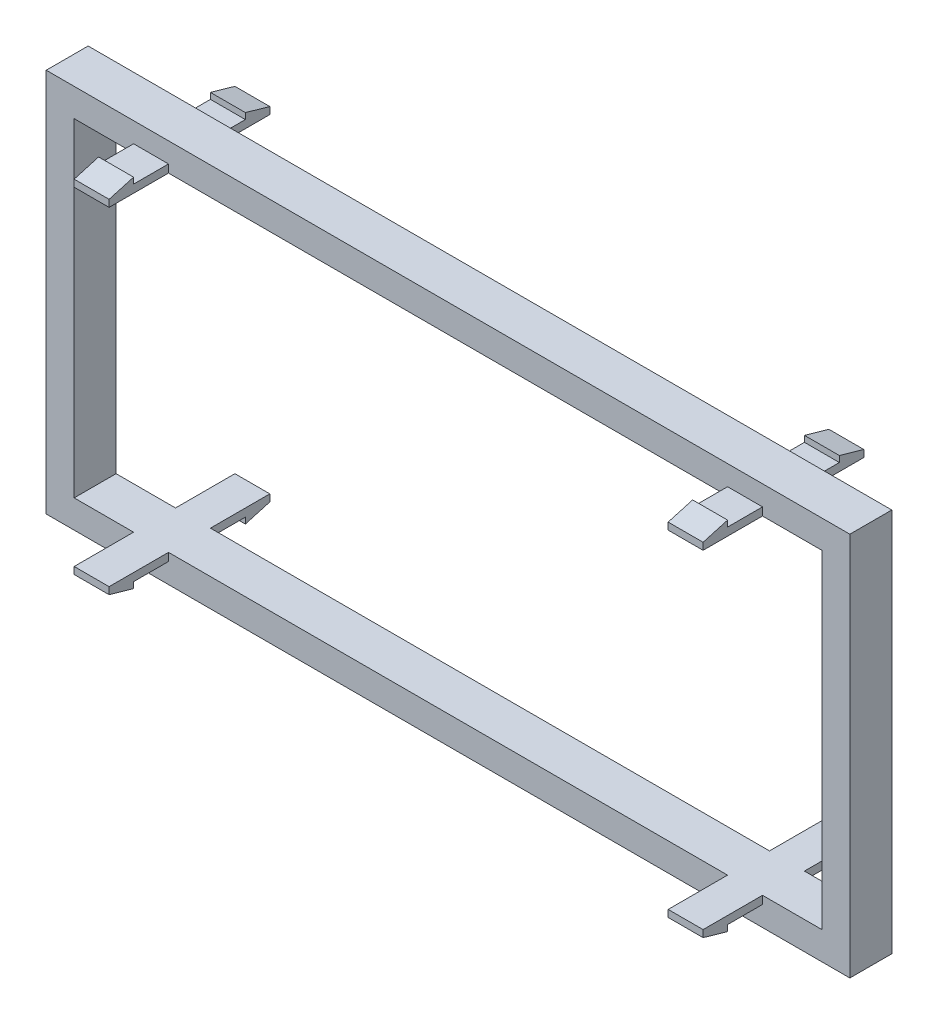
SolidWorks part; units mm, degrees
ref_plane "Front" through (0, 0, 0) normal (0, 0, 1) x (1, 0, 0)
ref_plane "Top" through (0, 0, 0) normal (0, 1, 0) x (1, 0, 0)
ref_plane "Right" through (0, 0, 0) normal (1, 0, 0) x (0, 0, -1)
sketch "Sketch1" plane through (0, 0, 0) normal (0, 0, 1) x (1, 0, 0)
  line L0 (0, 0) -> (0, 82.8716) construction
  line L1 (0, 0) -> (92.0509, 0) construction
  line L2 (-53.5, 23.5) -> (53.5, 23.5)
  line L3 (-57.5, 27.5) -> (57.5, 27.5)
  line L4 (-57.5, 27.5) -> (-57.5, -27.5)
  line L5 (-57.5, -27.5) -> (57.5, -27.5)
  line L6 (57.5, 27.5) -> (57.5, -27.5)
  line L7 (53.5, 23.5) -> (53.5, -23.5)
  line L8 (-53.5, -23.5) -> (53.5, -23.5)
  line L9 (-53.5, 23.5) -> (-53.5, -23.5)
  dimension "D1" = 115
  dimension "D2" = 55
  dimension "D3" = 4
extrude "Boss-Extrude1" add sketch "Sketch1" along normal blind 6
sketch "Sketch2" plane through (0, 0, 6) normal (0, 0, 1) x (1, 0, 0)
  line L0 (53.5, 23.5) -> (-53.5, 23.5) construction
  line L1 (-45, 25.5) -> (-40, 25.5)
  line L2 (-45, 25.5) -> (-45, 23.5)
  line L3 (-45, 23.5) -> (-40, 23.5)
  line L4 (-40, 25.5) -> (-40, 23.5)
  dimension "D1" = 2
  dimension "D2" = 45
  dimension "D3" = 40
extrude "Boss-Extrude2" add sketch "Sketch2" along normal blind 8.5
sketch "Sketch3" plane through (-40, 0, 0) normal (1, 0, 0) x (0, 0, -1)
  line L0 (-14.5, 24.5) -> (-11, 25.5)
  line L1 (-14.5, 23.5) -> (-14.5, 25.5) construction
  line L2 (-14.5, 25.5) -> (-6, 25.5) construction
  line L3 (-11, 25.5) -> (-11, 24.6338)
  line L4 (-11, 24.6338) -> (-6, 24.6338)
  line L5 (-6, 23.5) -> (-6, 25.5) construction
  line L6 (-6, 24.6338) -> (-6, 26.8746)
  line L7 (-6, -27.5) -> (-6, 27.5) construction
  line L8 (-6, 26.8746) -> (-14.5, 26.8746)
  line L9 (-14.5, 26.8746) -> (-14.5, 24.5)
  dimension "D1" = 5
extrude "Cut-Extrude1" cut sketch "Sketch3" against normal blind 10
mirror "Mirror1" about plane through (0, 0, 0) normal (0, 1, 0) of "Cut-Extrude1", "Boss-Extrude2"
mirror "Mirror2" about plane through (0, 0, 0) normal (1, 0, 0) of "Mirror1", "Boss-Extrude2", "Cut-Extrude1"
ref_plane "Plane1" through (0, 0, 3) normal (0, 0, 1) x (1, 0, 0)
mirror "Mirror3" about plane through (0, 0, 3) normal (0, 0, 1) of "Mirror2", "Boss-Extrude2", "Cut-Extrude1", "Mirror1"
sketch "Sketch4" plane through (0, 0, 0) normal (0, 1, 0) x (1, 0, 0)
  line L0 (0, -26.6432) -> (0, 29.2775) construction
equation "\"inlet_diameter\"= 30"
equation "\"total_length\"=200"
equation "\"outlet_length\"=80"
equation "\"outlet_diameter\"= 50"
equation "\"side_length\"=115"
equation "\"inlet_lentgh\"=80"
equation "\"flat_length\"=120"
equation "\"side_height\"=55"
equation "\"D1@Sketch1\"=\"side_length\""
equation "\"D2@Sketch1\"=\"side_height\""
